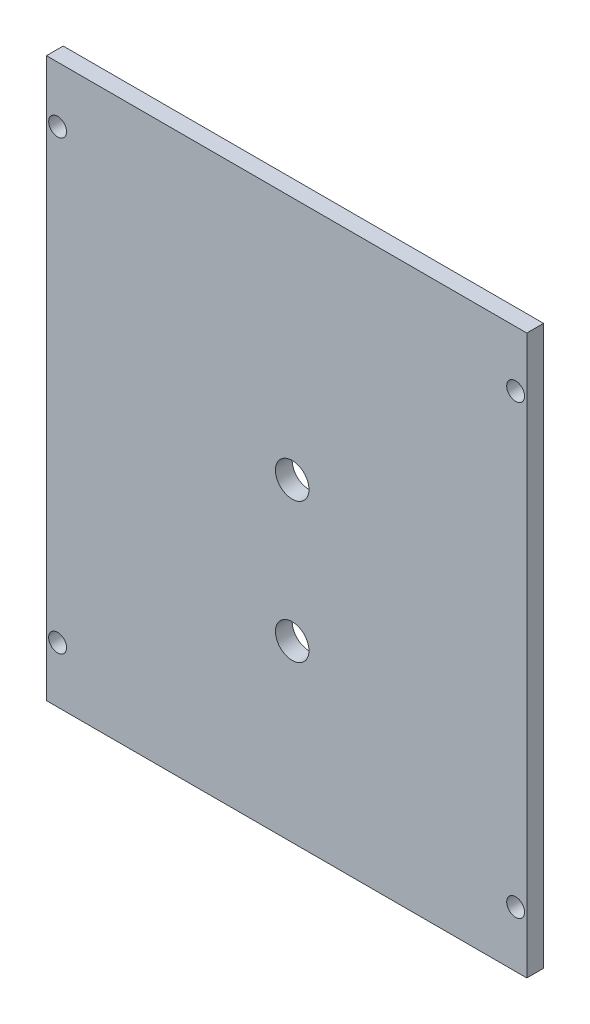
SolidWorks part; units mm, degrees
ref_plane "前视基准面" through (0, 0, 0) normal (0, 0, 1) x (1, 0, 0)
ref_plane "上视基准面" through (0, 0, 0) normal (0, 1, 0) x (1, 0, 0)
ref_plane "右视基准面" through (0, 0, 0) normal (1, 0, 0) x (0, 0, -1)
sketch "草图1" plane through (0, 0, 0) normal (0, 0, 1) x (1, 0, 0)
  line L1 (0, 0) -> (84, 0)
  line L2 (0, 0) -> (0, 100)
  line L3 (0, 100) -> (84, 100)
  line L4 (84, 0) -> (84, 100)
  dimension "D1" = 84
  dimension "D2" = 100
extrude "凸台-拉伸1" add sketch "草图1" along normal blind 3
sketch "草图3" plane through (0, 0, 3) normal (0, 0, 1) x (1, 0, 0)
  line L0 (42, 0) -> (42, 100) construction
  line L1 (0, 0) -> (84, 0) construction
  line L2 (84, 100) -> (0, 100) construction
  circle A0 centre (42, 31.24) radius 3
  circle A1 centre (42, 56.24) radius 3
  dimension "D1" = 6
  dimension "D3" = 6
  dimension "D2" = 31.24
  dimension "D4" = 25
extrude "切除-拉伸1" cut sketch "草图3" against normal blind 3
sketch "草图4" plane through (0, 0, 0) normal (-1, 0, 0) x (0, 0, 1)
  line L1 (0, 0) -> (3, 0)
  line L2 (0, 0) -> (0, 100)
  line L3 (0, 100) -> (3, 100)
  line L4 (3, 0) -> (3, 100)
extrude "凸台-拉伸2" add sketch "草图4" along normal blind 2
sketch "草图5" plane through (0, 0, 3) normal (0, 0, 1) x (1, 0, 0)
  line L0 (82, 5.5942) -> (82, 49.7023) construction
  line L1 (84, 0) -> (84, 100) construction
  line L2 (-2, 0) -> (84, 0) construction
  line L3 (-2, 50) -> (63.1725, 50) construction
  line L4 (-2, 0) -> (-2, 100) construction
  line L5 (41, 0) -> (41, 73.3633) construction
  circle A0 centre (82, 10) radius 1.6
  circle A1 centre (82, 90) radius 1.6
  circle A2 centre (0, 90) radius 1.6
  circle A3 centre (0, 10) radius 1.6
  dimension "D1" = 3.2
  dimension "D2" = 2
  dimension "D3" = 10
extrude "切除-拉伸2" cut sketch "草图5" against normal through all
